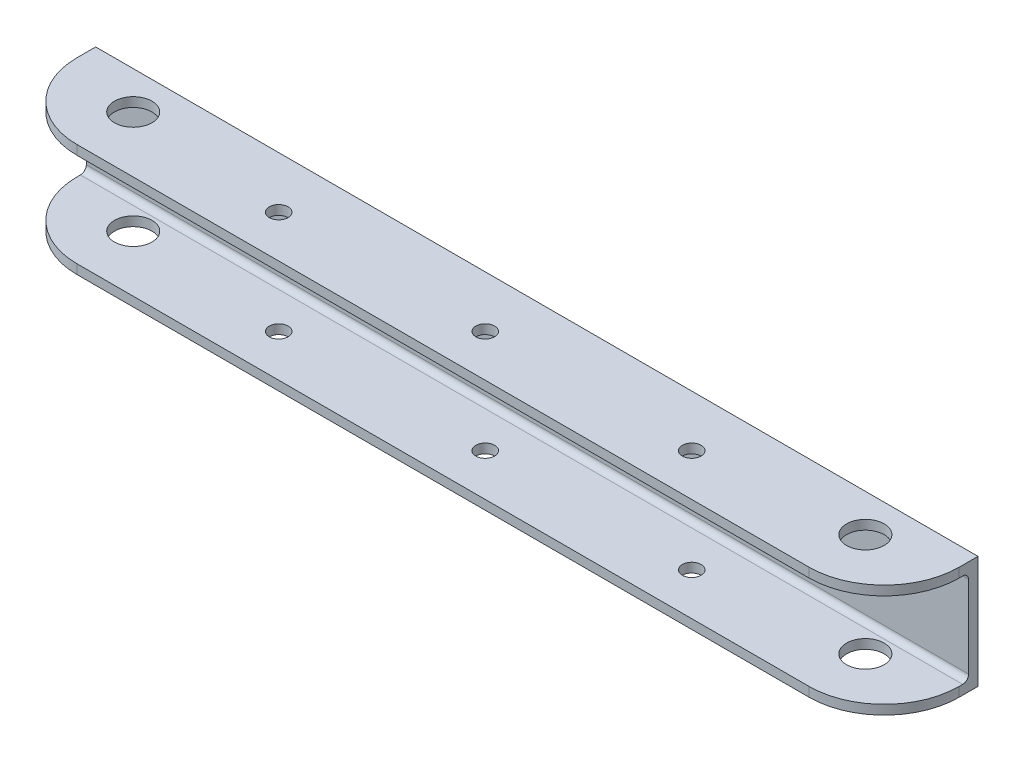
SolidWorks part; units mm, degrees
ref_plane "Front Plane" through (0, 0, 0) normal (0, 0, 1) x (1, 0, 0)
ref_plane "Top Plane" through (0, 0, 0) normal (0, 1, 0) x (1, 0, 0)
ref_plane "Right Plane" through (0, 0, 0) normal (1, 0, 0) x (0, 0, -1)
sketch "Sketch1" plane through (0, 0, 0) normal (0, 0, 1) x (1, 0, 0)
  line L1 (-288.2759, 0) -> (-339.0759, 0)
  line L2 (-288.2759, 0) -> (-288.2759, 38.1)
  line L3 (-288.2759, 38.1) -> (-339.0759, 38.1)
  line L4 (-339.0759, 0) -> (-339.0759, 38.1)
  line L6 (-313.6759, 0) -> (-313.6759, 38.1) construction
  line L8 (-535.9259, 0) -> (-586.7259, 0)
  line L9 (-535.9259, 0) -> (-535.9259, 38.1)
  line L10 (-535.9259, 38.1) -> (-586.7259, 38.1)
  line L11 (-586.7259, 0) -> (-586.7259, 38.1)
  line L12 (-561.3259, 0) -> (-561.3259, 38.1) construction
  line L13 (-561.3259, 1463.04) -> (-561.3259, 38.1) construction
  line L15 (-313.6759, 38.1) -> (-313.6759, 1463.04) construction
  line L16 (-535.9259, 38.1) -> (-339.0759, 38.1)
  line L17 (-605.7759, 1463.04) -> (-516.8759, 1463.04)
  line L18 (-605.7759, 1463.04) -> (-605.7759, 1424.94)
  line L19 (-605.7759, 1424.94) -> (-516.8759, 1424.94)
  line L20 (-516.8759, 1463.04) -> (-516.8759, 1424.94)
  line L21 (-358.1259, 1463.04) -> (-269.2259, 1463.04)
  line L22 (-358.1259, 1463.04) -> (-358.1259, 1424.94)
  line L23 (-358.1259, 1424.94) -> (-269.2259, 1424.94)
  line L24 (-269.2259, 1463.04) -> (-269.2259, 1424.94)
  line L25 (-535.9259, 0) -> (-339.0759, 0)
  point P31 (-269.2259, 1443.99)
  point P32 (-313.6759, 1463.04)
  dimension "D1" = 50.8
  dimension "D3" = 50.8
  dimension "D4" = 38.1
  dimension "D5" = 247.65
  dimension "D6" = 88.9
  dimension "D7" = 44.45
  dimension "D8" = 38.1
  dimension "D9" = 38.1
  dimension "D10" = 88.9
extrude "Boss-Extrude1" add sketch "Sketch1" along normal blind 31.75 contours L11 L8 L9 L10 | L9 L25 L4 L16 | L4 L1 L2 L3
sketch "Sketch2" plane through (-586.7259, 0, 0) normal (-1, 0, 0) x (0, 0, 1)
  line L1 (31.75, 34.925) -> (3.175, 34.925)
  line L2 (31.75, 34.925) -> (31.75, 3.175)
  line L3 (31.75, 3.175) -> (3.175, 3.175)
  line L4 (3.175, 34.925) -> (3.175, 3.175)
  line L6 (31.75, 0) -> (0, 0) construction
  line L16 (0, 0) -> (0, 38.1) construction
  line L17 (31.75, 38.1) -> (0, 38.1) construction
  line L18 (31.75, 0) -> (31.75, 38.1) construction
  dimension "D1" = 3.175
  dimension "D2" = 3.175
  dimension "D3" = 3.175
extrude "Cut-Extrude1" cut sketch "Sketch2" against normal through all
sketch "Sketch3" plane through (0, 0, 0) normal (0, -1, 0) x (1, 0, 0)
  line L0 (-388.0987, 0) -> (-508.3835, 0) construction
  line L1 (-437.5009, 12.7) -> (-437.5009, 31.75) construction
  line L3 (-288.2759, 31.75) -> (-586.7259, 31.75) construction
  line L5 (-561.3259, 12.7) -> (-313.6759, 12.7) construction
  circle A0 centre (-561.3259, 12.7) radius 6.35
  circle A1 centre (-313.6759, 12.7) radius 6.35
  dimension "D5" = 12.7
  dimension "D6" = 12.7
  dimension "D1" = 12.7
  dimension "D4" = 247.65
extrude "Cut-Extrude2" cut sketch "Sketch3" against normal through all
fillet "Fillet1" radius 25.4 4 edges at (-288.2759, 36.5125, 31.75) (-288.2759, 1.5875, 31.75) (-586.7259, 1.5875, 31.75) (-586.7259, 36.5125, 31.75)
sketch "Sketch4" plane through (0, 0, 0) normal (0, -1, 0) x (1, 0, 0)
  circle A0 centre (-507.3509, 17.4625) radius 3.175
  circle A1 centre (-437.5009, 17.4625) radius 3.175
  circle A2 centre (-367.6509, 17.4625) radius 3.175
  dimension "D1" = 6.35
extrude "Cut-Extrude3" cut sketch "Sketch4" against normal through all
fillet "Fillet2" radius 2 2 edges at (-437.5009, 3.175, 3.175) (-437.5009, 34.925, 3.175)
